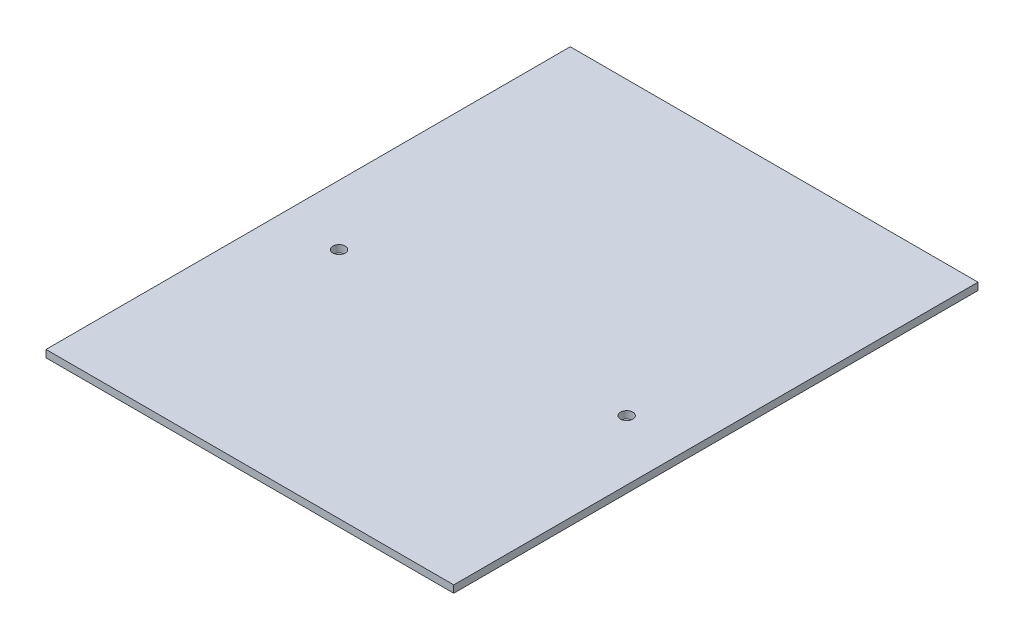
SolidWorks part; units mm, degrees
material "PC High Viscosity"
ref_plane "Front Plane" through (0, 0, 0) normal (0, 0, 1) x (1, 0, 0)
ref_plane "Top Plane" through (0, 0, 0) normal (0, 1, 0) x (1, 0, 0)
ref_plane "Right Plane" through (0, 0, 0) normal (1, 0, 0) x (0, 0, -1)
sketch "Sketch1" plane through (0, 0, 0) normal (0, 1, 0) x (1, 0, 0)
  line L1 (0, 0) -> (355.6, 0)
  line L2 (0, 0) -> (0, 457.2)
  line L3 (0, 457.2) -> (355.6, 457.2)
  line L4 (355.6, 0) -> (355.6, 457.2)
  dimension "D1" = 355.6
  dimension "D2" = 457.2
extrude "Boss-Extrude1" add sketch "Sketch1" along normal blind 6.35
hole_wizard "27/64 (0.42188) Diameter Hole1" positions "Sketch2" profile "Sketch3" hole size "27/64" standard "ANSI Inch" end condition through all
sketch "Sketch2" plane through (0, 6.35, 0) normal (0, 1, 0) x (1, 0, 0)
  line L0 (44.45, 0) -> (44.45, 457.2) construction
  line L1 (0, 0) -> (355.6, 0) construction
  line L2 (355.6, 457.2) -> (0, 457.2) construction
  line L3 (177.8, 0) -> (177.8, 457.2) construction
  line L4 (0, 457.2) -> (0, 0) construction
  point P8 (52.3875, 203.2)
  point P15 (303.2125, 203.2)
  dimension "D1" = 44.45
  dimension "D2" = 7.9375
  dimension "D3" = 254
sketch "Sketch3" plane through (303.2125, 6.35, -203.2) normal (1, 0, 0) x (0, 0, 1)
  line L0 (0, 0) -> (0, 6.35)
  line L1 (0, 6.35) -> (5.3579, 6.35)
  line L2 (5.3579, 6.35) -> (5.3579, 0)
  line L5 (5.3579, 0) -> (0, 0)
  line L11 (0, -6.35) -> (0, 107.95) construction
  dimension "Thru Hole Dia." = 10.7158
  dimension "Thru Hole Depth" = 6.35
